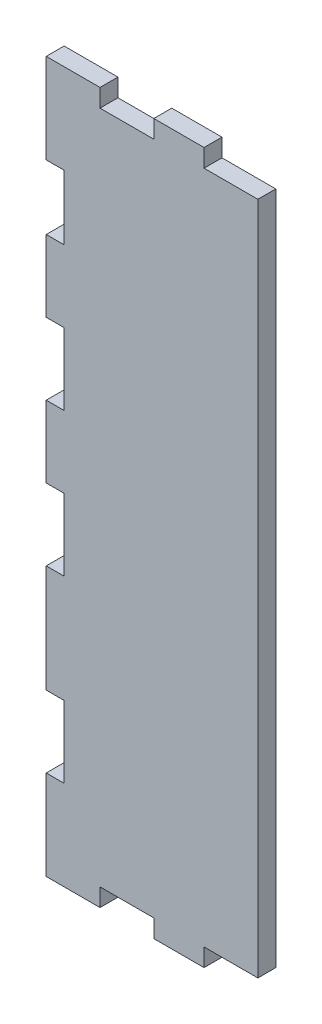
SolidWorks part; units mm, degrees
ref_plane "Front Plane" through (0, 0, 0) normal (0, 0, 1) x (1, 0, 0)
ref_plane "Top Plane" through (0, 0, 0) normal (0, 1, 0) x (1, 0, 0)
ref_plane "Right Plane" through (0, 0, 0) normal (1, 0, 0) x (0, 0, -1)
sketch "Sketch1" plane through (0, 0, 0) normal (0, 0, 1) x (1, 0, 0)
  line L0 (-69.85, 1.27) -> (-69.85, 252.73) construction
  line L1 (0, 1.27) -> (-69.85, 1.27)
  line L2 (0, 1.27) -> (0, 252.73)
  line L3 (0, 252.73) -> (-69.85, 252.73)
  line L6 (-76.2, 1.27) -> (-69.85, 1.27)
  line L7 (-76.2, 1.27) -> (-76.2, 252.73)
  line L8 (-76.2, 252.73) -> (-69.85, 252.73)
extrude "Boss-Extrude1" add sketch "Sketch1" along normal blind 6.35
sketch "Sketch3" plane through (0, 252.73, 0) normal (0, 1, 0) x (1, 0, 0)
  line L0 (0, 0) -> (-76.2, 0) construction
  line L1 (-55.88, 0) -> (-36.83, 0)
  line L2 (-55.88, 0) -> (-55.88, -6.35)
  line L3 (-55.88, -6.35) -> (-36.83, -6.35)
  line L4 (-36.83, 0) -> (-36.83, -6.35)
  line L5 (0, -6.35) -> (-76.2, -6.35) construction
  line L6 (0, -6.35) -> (0, 0) construction
  line L7 (-19.05, 0) -> (0, 0)
  line L8 (-19.05, 0) -> (-19.05, -6.35)
  line L9 (-19.05, -6.35) -> (0, -6.35)
  line L10 (0, 0) -> (0, -6.35)
  line L11 (-19.05, -6.35) -> (-19.05, 0) construction
  line L14 (-76.2, -6.35) -> (-74.93, -6.35)
  line L15 (-76.2, -6.35) -> (-76.2, 0)
  line L16 (-76.2, 0) -> (-74.93, 0)
  line L17 (-74.93, -6.35) -> (-74.93, 0)
  point P14 (0, -3.175)
  line M6 (0, 0) -> (-76.2, 0)
  line M8 (-76.2, -6.35) -> (0, -6.35)
  line M9 (0, -6.35) -> (0, 0)
  dimension "D1" = 0
  dimension "D2" = 19.05
  dimension "D3" = 17.78
  dimension "D4" = 19.05
  dimension "D5" = 19.05
extrude "Cut-Extrude1" cut sketch "Sketch3" against normal blind 6.35 contours L4 L2 M6 M8 | L8 M6 M8 M9
sketch "Sketch4" plane through (0, 252.73, 0) normal (0, 1, 0) x (1, 0, 0)
  line L0 (-55.88, 0) -> (-76.2, 0) construction
  line L1 (-76.2, -6.35) -> (-74.93, -6.35)
  line L2 (-76.2, -6.35) -> (-76.2, 0)
  line L3 (-76.2, 0) -> (-74.93, 0)
  line L4 (-74.93, -6.35) -> (-74.93, 0)
  line L5 (-55.88, 0) -> (-55.88, -6.35) construction
  dimension "D1" = 19.05
extrude "Cut-Extrude2" cut sketch "Sketch4" against normal through all
sketch "Sketch5" plane through (0, 1.27, 0) normal (0, -1, 0) x (1, 0, 0)
  line L0 (-74.93, 6.35) -> (0, 6.35) construction
  line L1 (-36.83, 6.35) -> (-55.88, 6.35)
  line L2 (-36.83, 6.35) -> (-36.83, 0)
  line L3 (-36.83, 0) -> (-55.88, 0)
  line L4 (-55.88, 6.35) -> (-55.88, 0)
  line L5 (-74.93, 0) -> (0, 0) construction
  line L6 (0, 6.35) -> (0, 0) construction
  line L7 (0, 6.35) -> (-19.05, 6.35)
  line L8 (0, 6.35) -> (0, 0)
  line L9 (0, 0) -> (-19.05, 0)
  line L10 (-19.05, 6.35) -> (-19.05, 0)
  dimension "D1" = 0
  dimension "D2" = 19.05
  dimension "D3" = 17.78
  dimension "D4" = 19.05
extrude "Cut-Extrude3" cut sketch "Sketch5" against normal blind 6.35
sketch "Sketch6" plane through (0, 0, 6.35) normal (0, 0, 1) x (1, 0, 0)
  line L0 (-74.93, 1.27) -> (-74.93, 252.73) construction
  line L1 (-74.93, 33.02) -> (-68.58, 33.02)
  line L2 (-74.93, 33.02) -> (-74.93, 58.42)
  line L3 (-74.93, 58.42) -> (-68.58, 58.42)
  line L4 (-68.58, 33.02) -> (-68.58, 58.42)
  line L5 (-74.93, 1.27) -> (-55.88, 1.27) construction
  line L6 (-74.93, 96.52) -> (-68.58, 96.52)
  line L7 (-74.93, 96.52) -> (-74.93, 121.92)
  line L8 (-74.93, 121.92) -> (-68.58, 121.92)
  line L9 (-68.58, 96.52) -> (-68.58, 121.92)
  line L10 (-74.93, 147.32) -> (-68.58, 147.32)
  line L11 (-74.93, 147.32) -> (-74.93, 172.72)
  line L12 (-74.93, 172.72) -> (-68.58, 172.72)
  line L13 (-68.58, 147.32) -> (-68.58, 172.72)
  line L14 (-55.88, 252.73) -> (-74.93, 252.73) construction
  line L15 (-74.93, 198.12) -> (-68.58, 198.12)
  line L16 (-74.93, 198.12) -> (-74.93, 220.98)
  line L17 (-74.93, 220.98) -> (-68.58, 220.98)
  line L18 (-68.58, 198.12) -> (-68.58, 220.98)
  dimension "D1" = 25.4
  dimension "D2" = 25.4
  dimension "D3" = 31.75
  dimension "D4" = 38.1
  dimension "D5" = 25.4
  dimension "D6" = 25.4
  dimension "D7" = 25.4
  dimension "D8" = 31.75
  dimension "D9" = 22.86
  dimension "D10" = 6.35
  dimension "D11" = 6.35
  dimension "D12" = 6.35
  dimension "D13" = 6.35
extrude "Cut-Extrude4" cut sketch "Sketch6" against normal blind 6.35
